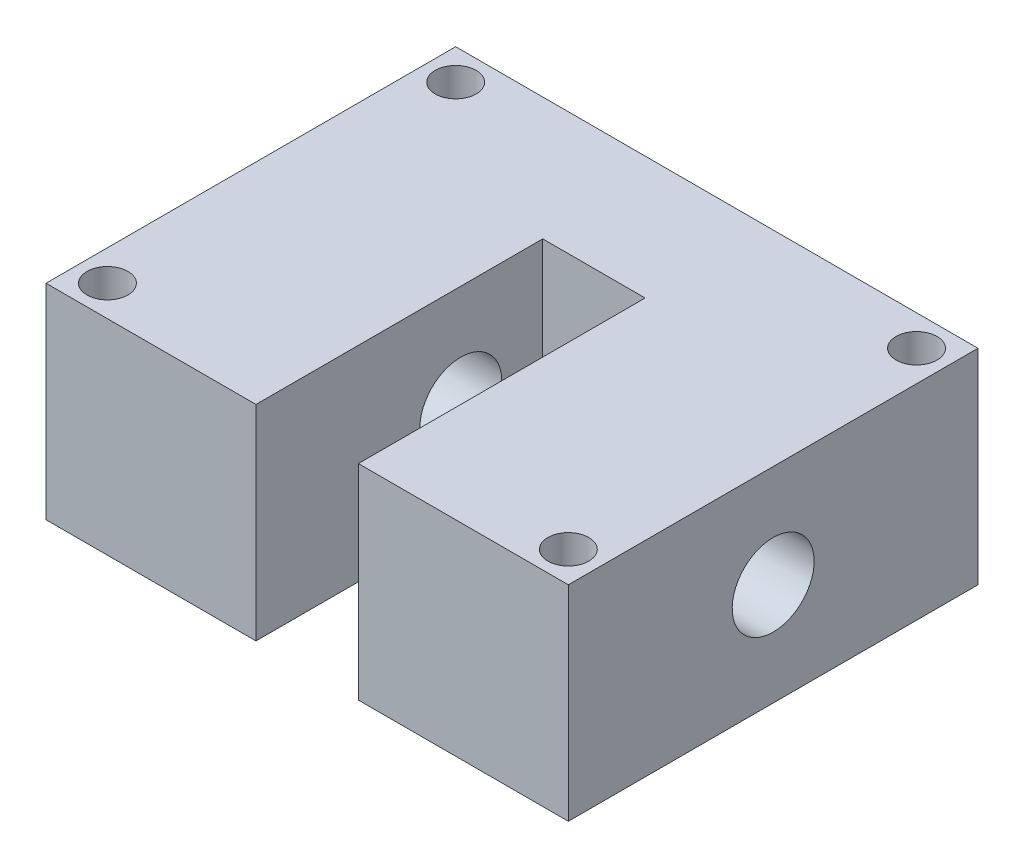
SolidWorks part; units mm, degrees
ref_plane "前视基准面" through (0, 0, 0) normal (0, 0, 1) x (1, 0, 0)
ref_plane "上视基准面" through (0, 0, 0) normal (0, 1, 0) x (1, 0, 0)
ref_plane "右视基准面" through (0, 0, 0) normal (1, 0, 0) x (0, 0, -1)
sketch "草图1" plane through (0, 0, 0) normal (0, 0, 1) x (1, 0, 0)
  line L1 (-25.5, 10) -> (25.5, 10)
  line L2 (-25.5, 10) -> (-25.5, -10)
  line L3 (-25.5, -10) -> (25.5, -10)
  line L4 (25.5, 10) -> (25.5, -10)
  line L5 (-25.5, 10) -> (25.5, -10) construction
  line L6 (-25.5, -10) -> (25.5, 10) construction
  point P0 (0, 0)
  dimension "D1" = 51
  dimension "D2" = 20
extrude "凸台-拉伸1" add sketch "草图1" along normal mid plane 40
sketch "草图2" plane through (0, 0, 20) normal (0, 0, 1) x (1, 0, 0)
  line L1 (-5, 10) -> (5, 10)
  line L2 (-5, 10) -> (-5, -10)
  line L3 (-5, -10) -> (5, -10)
  line L4 (5, 10) -> (5, -10)
  line L5 (-5, 10) -> (5, -10) construction
  line L6 (-5, -10) -> (5, 10) construction
  point P0 (0, 0)
  dimension "D1" = 20
  dimension "D2" = 10
extrude "切除-拉伸1" cut sketch "草图2" against normal blind 28
sketch "草图3" plane through (-25.5, 0, 0) normal (-1, 0, 0) x (0, 0, 1)
  circle A0 centre (0, 0) radius 4
  point P2 (0, 0)
  point P3 (0, 0)
  dimension "D1" = 8
extrude "切除-拉伸2" cut sketch "草图3" against normal through all both and the other way through all
sketch "草图4" plane through (0, 10, 0) normal (0, 1, 0) x (1, 0, 0)
  line L20 (-5, -17) -> (-22.5, -17)
  line L21 (22.5, -17) -> (5, -17)
  line L22 (22.5, 17) -> (22.5, -17)
  line L23 (-22.5, 17) -> (22.5, 17)
  line L24 (-22.5, -17) -> (-22.5, 17)
  line L25 (-5, -17) -> (-22.5, -17) construction
  line L26 (22.5, -17) -> (5, -17) construction
  line L27 (22.5, 17) -> (22.5, -17) construction
  line L28 (-22.5, 17) -> (22.5, 17) construction
  line L29 (-22.5, -17) -> (-22.5, 17) construction
  circle A0 centre (-22.5, 17) radius 2
  circle A1 centre (22.5, -17) radius 2
  circle A2 centre (22.5, 17) radius 2
  circle A3 centre (-22.5, -17) radius 2
  dimension "D1" = 3
extrude "切除-拉伸3" cut sketch "草图4" against normal through all
